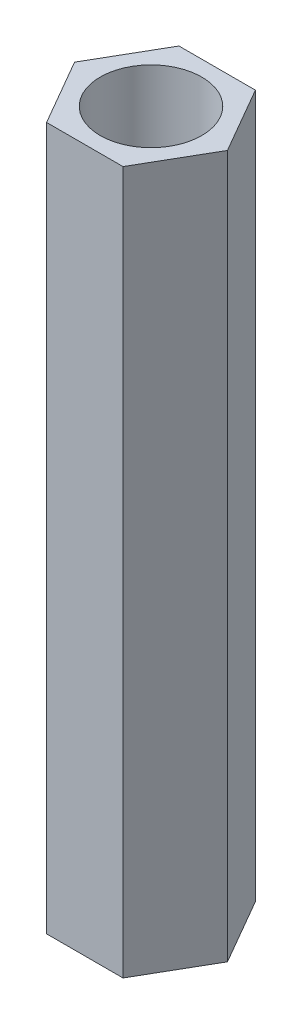
SolidWorks part; units mm, degrees
ref_plane "Front Plane" through (0, 0, 0) normal (0, 0, 1) x (1, 0, 0)
ref_plane "Top Plane" through (0, 0, 0) normal (0, 1, 0) x (1, 0, 0)
ref_plane "Right Plane" through (0, 0, 0) normal (1, 0, 0) x (0, 0, -1)
sketch "Sketch1" plane through (0, 0, 0) normal (0, 1, 0) x (1, 0, 0)
  line L1 (0.979, -1.6957) -> (1.958, 0)
  line L2 (1.958, 0) -> (0.979, 1.6957)
  line L3 (0.979, 1.6957) -> (-0.979, 1.6957)
  line L4 (-0.979, 1.6957) -> (-1.958, 0)
  line L5 (-1.958, 0) -> (-0.979, -1.6957)
  line L6 (-0.979, -1.6957) -> (0.979, -1.6957)
  circle A0 centre (0, 0) radius 1.6957 construction
  circle A1 centre (0, 0) radius 1.3
  dimension "D1" = 2.6
extrude "Boss-Extrude1" add sketch "Sketch1" along normal blind 18
